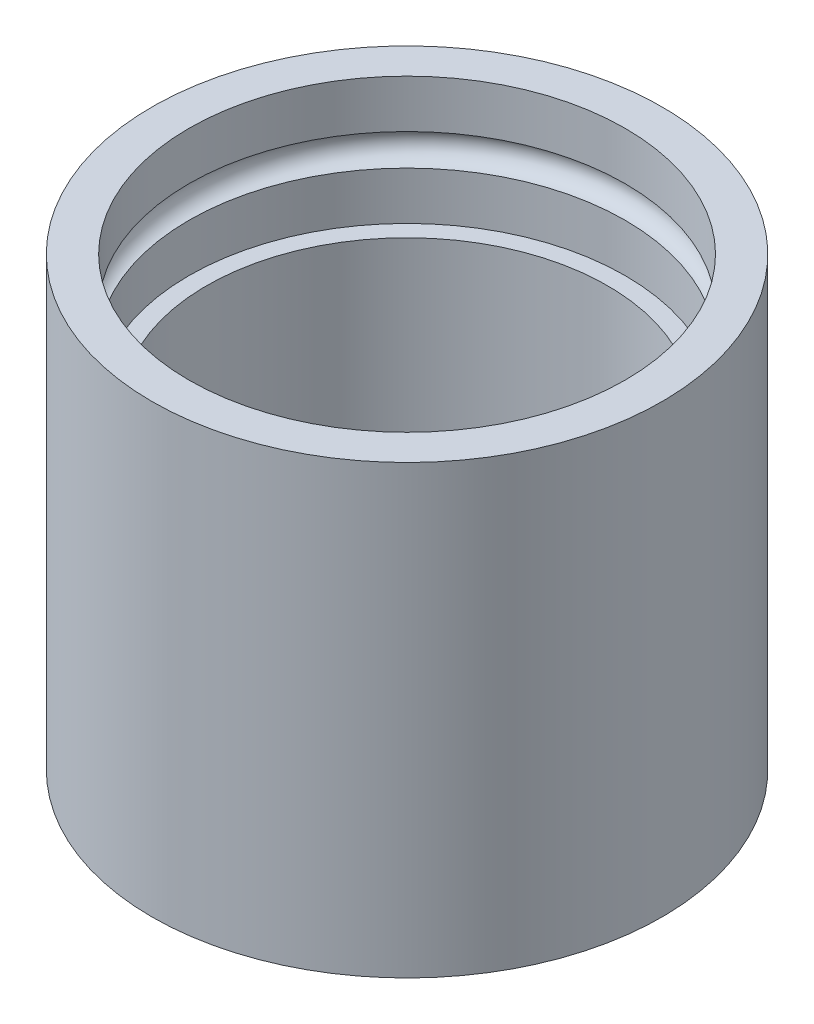
SolidWorks part; units mm, degrees
ref_plane "Front Plane" through (0, 0, 0) normal (0, 0, 1) x (1, 0, 0)
ref_plane "Top Plane" through (0, 0, 0) normal (0, 1, 0) x (1, 0, 0)
ref_plane "Right Plane" through (0, 0, 0) normal (1, 0, 0) x (0, 0, -1)
sketch "Sketch1" plane through (0, 0, 0) normal (1, 0, 0) x (0, 0, -1)
  line L0 (0, 0) -> (0, -88.9)
  line L1 (0, -88.9) -> (10.16, -88.9)
  line L2 (10.8585, -76.2) -> (10.8585, -25.4038)
  line L3 (10.8585, -25.4038) -> (7.366, -25.4038)
  line L4 (7.366, -25.4038) -> (7.366, -15.8574)
  line L5 (7.366, -9.5503) -> (7.366, 0)
  line L6 (7.366, 0) -> (0, 0)
  line L7 (50.8, -28.3132) -> (50.8, -103.0735) construction
  line L9 (10.8585, -76.2) -> (18.4785, -76.2)
  line L10 (18.4785, -76.2) -> (18.4785, -88.9)
  line L11 (18.4785, -88.9) -> (10.16, -88.9)
  arc A0 (7.366, -15.8574) -> (7.366, -9.5503) centre (7.7343, -12.7038) cw
  dimension "D6" = 3.175
  dimension "D1" = 88.9
  dimension "D2" = 63.5
  dimension "D4" = 12.7
  dimension "D5" = 10.16
  dimension "D7" = 50.8
  dimension "D9" = 7.62
  dimension "D10" = 12.7
  dimension "D11" = 0.3683
  dimension "D3" = 3.4925
  dimension "D8" = 7.366
  dimension "D12" = 7.366
revolve "Revolve1" add sketch "Sketch1" angle 360 about L7
equation "\"D12@Sketch1\"=\"D8@Sketch1\""
